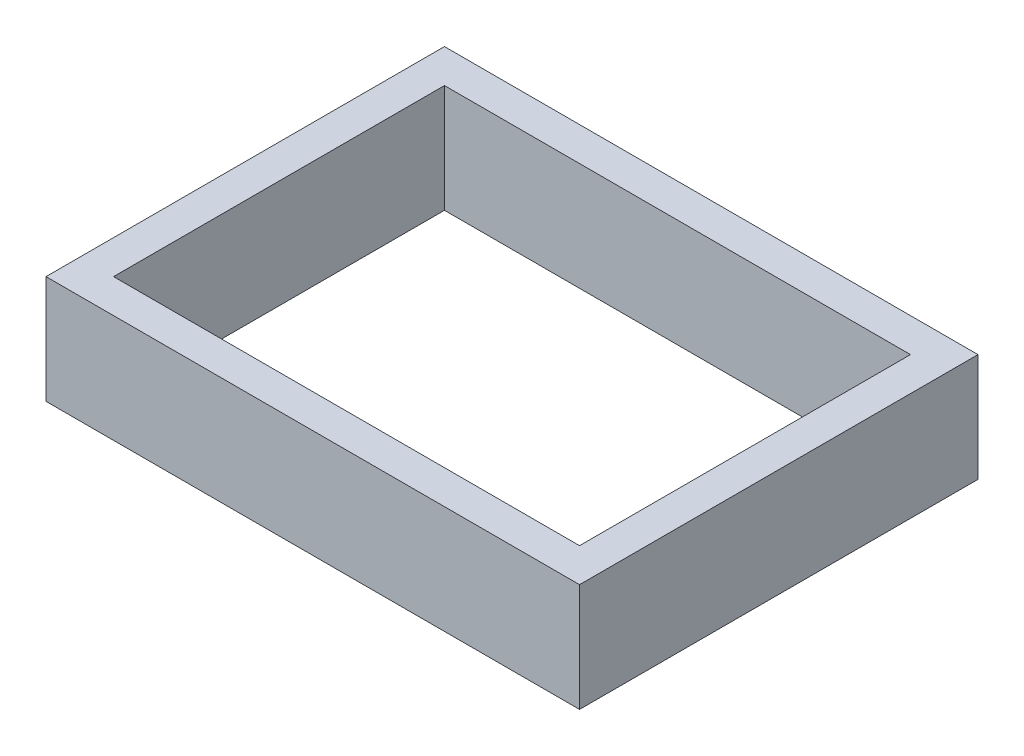
SolidWorks part; units mm, degrees
ref_plane "Front Plane" through (0, 0, 0) normal (0, 0, 1) x (1, 0, 0)
ref_plane "Top Plane" through (0, 0, 0) normal (0, 1, 0) x (1, 0, 0)
ref_plane "Right Plane" through (0, 0, 0) normal (1, 0, 0) x (0, 0, -1)
ref_plane "Plane1" through (0, 101.6, 0) normal (0, 1, 0) x (1, 0, 0)
sketch "Sketch1" plane through (0, 101.6, 0) normal (0, 1, 0) x (1, 0, 0)
  line L1 (0, 0) -> (-876.3, 0)
  line L2 (0, 0) -> (0, 622.3)
  line L3 (0, 622.3) -> (-876.3, 622.3)
  line L4 (-876.3, 0) -> (-876.3, 622.3)
  line L5 (63.5, -63.5) -> (-939.8, -63.5)
  line L6 (63.5, -63.5) -> (63.5, 685.8)
  line L7 (63.5, 685.8) -> (-939.8, 685.8)
  line L8 (-939.8, -63.5) -> (-939.8, 685.8)
  dimension "D1" = 622.3
  dimension "D2" = 876.3
  dimension "D3" = 63.5
  dimension "D4" = 63.5
  dimension "D5" = 63.5
  dimension "D6" = 63.5
extrude "Boss-Extrude1" add sketch "Sketch1" along normal blind 203.2
equation "\"sheet width\"= .19"
equation "\"width\"= 24.5"
equation "\"length\"= 34.5"
equation "\"standoff hole size\"= .5"
equation "\"ground clearence\"= 3"
equation "\"small drive pulley\"= 74.55mm"
equation "\"large drive pulley\"= 150.95mm"
equation "\"drive axle hole size\"= .5"
equation "\"front pulley clearence\"= 1"
equation "\"center support location\"= 19"
equation "\"inner to outer wall size\"= 3.75"
equation "\"D1@Sketch1\"=\"width\""
equation "\"D2@Sketch1\"=\"length\""
